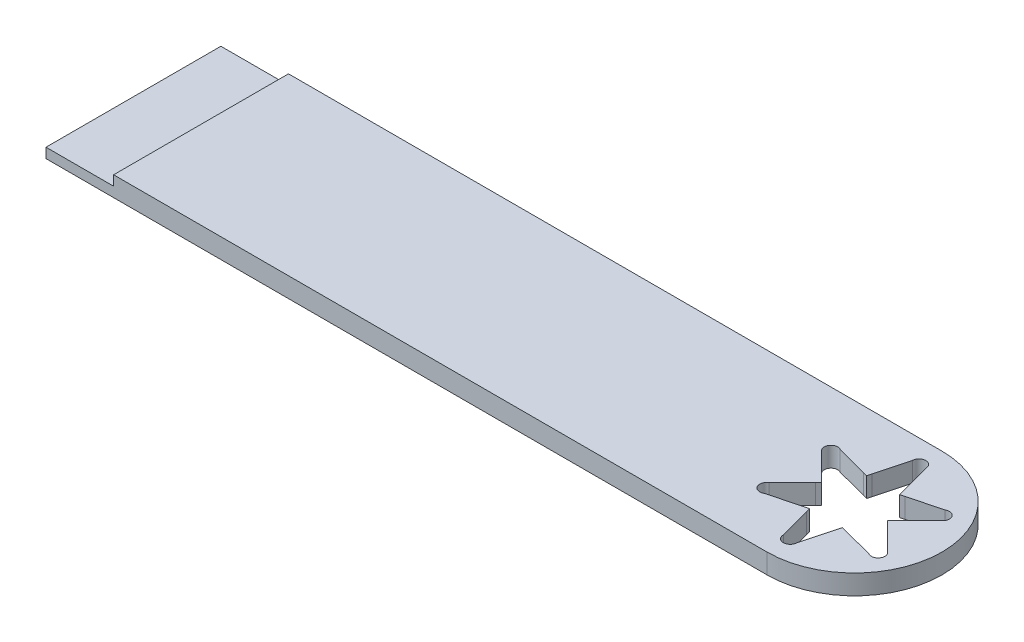
SolidWorks part; units mm, degrees
ref_plane "前基準面" through (0, 0, 0) normal (0, 0, 1) x (1, 0, 0)
ref_plane "上基準面" through (0, 0, 0) normal (0, 1, 0) x (1, 0, 0)
ref_plane "右基準面" through (0, 0, 0) normal (1, 0, 0) x (0, 0, -1)
sketch "草圖1" plane through (0, 0, 0) normal (0, 1, 0) x (1, 0, 0)
  circle A0 centre (0, 0) radius 15.8
  dimension "D1" = 31.6
extrude "填料-伸長1" add sketch "草圖1" along normal blind 4.4
sketch "草圖3" plane through (0, 0, 0) normal (0, -1, 0) x (1, 0, 0)
  line L0 (0, 15.8) -> (0, 15.7286) construction
  line L5 (0, 15.8) -> (0, 15.7286) construction
  line L9 (-1.5, 14.3) -> (-3.4, 7.2726)
  line L10 (-3.4, 7.2726) -> (-3.6501, 6.3221)
  line L13 (1.5, 14.3) -> (3.4, 7.2726)
  line L14 (3.4, 7.2726) -> (3.6501, 6.3221)
  line L15 (11.6342, 8.449) -> (4.5982, 6.5808)
  line L16 (13.1342, 5.851) -> (7.9982, 0.6918)
  line L17 (4.5982, 6.5808) -> (3.6501, 6.3221)
  line L18 (7.9982, 0.6918) -> (7.3001, 0)
  line L19 (13.1342, -5.851) -> (7.9982, -0.6918)
  line L20 (11.6342, -8.449) -> (4.5982, -6.5808)
  line L21 (7.9982, -0.6918) -> (7.3001, 0)
  line L22 (4.5982, -6.5808) -> (3.6501, -6.3221)
  line L23 (1.5, -14.3) -> (3.4, -7.2726)
  line L24 (-1.5, -14.3) -> (-3.4, -7.2726)
  line L25 (3.4, -7.2726) -> (3.6501, -6.3221)
  line L26 (-3.4, -7.2726) -> (-3.6501, -6.3221)
  line L27 (-11.6342, -8.449) -> (-4.5982, -6.5808)
  line L28 (-13.1342, -5.851) -> (-7.9982, -0.6918)
  line L29 (-4.5982, -6.5808) -> (-3.6501, -6.3221)
  line L30 (-7.9982, -0.6918) -> (-7.3001, 0)
  line L31 (-13.1342, 5.851) -> (-7.9982, 0.6918)
  line L32 (-11.6342, 8.449) -> (-4.5982, 6.5808)
  line L33 (-7.9982, 0.6918) -> (-7.3001, 0)
  line L34 (-4.5982, 6.5808) -> (-3.6501, 6.3221)
  circle A1 centre (0, 0) radius 15.8 construction
  arc A2 (0, 15.8) -> (-1.5, 14.3) centre (0, 14.3) ccw
  arc A3 (0, 15.8) -> (1.5, 14.3) centre (0, 14.3) cw
  arc A4 (13.6832, 7.9) -> (11.6342, 8.449) centre (12.3842, 7.15) ccw
  arc A5 (13.6832, 7.9) -> (13.1342, 5.851) centre (12.3842, 7.15) cw
  arc A6 (13.6832, -7.9) -> (13.1342, -5.851) centre (12.3842, -7.15) ccw
  arc A7 (13.6832, -7.9) -> (11.6342, -8.449) centre (12.3842, -7.15) cw
  arc A8 (0, -15.8) -> (1.5, -14.3) centre (0, -14.3) ccw
  arc A9 (0, -15.8) -> (-1.5, -14.3) centre (0, -14.3) cw
  arc A10 (-13.6832, -7.9) -> (-11.6342, -8.449) centre (-12.3842, -7.15) ccw
  arc A11 (-13.6832, -7.9) -> (-13.1342, -5.851) centre (-12.3842, -7.15) cw
  arc A12 (-13.6832, 7.9) -> (-13.1342, 5.851) centre (-12.3842, 7.15) ccw
  arc A13 (-13.6832, 7.9) -> (-11.6342, 8.449) centre (-12.3842, 7.15) cw
  point P12 (0, 14.3)
  point P69 (0, 0)
  dimension "D2" = 1.5
  dimension "D5" = 1.5
  dimension "D6" = 6
extrude "除料-伸長2" cut sketch "草圖3" against normal blind 4.4
sketch "草圖4" plane through (0, 0, 0) normal (0, 1, 0) x (1, 0, 0)
  circle A0 centre (0, 0) radius 15.8
  circle A1 centre (0, 0) radius 19.4
extrude "填料-伸長2" add sketch "草圖4" along normal blind 4.4
sketch "草圖5" plane through (0, 4.4, 0) normal (0, 1, 0) x (1, 0, 0)
  line L0 (0, 19.4) -> (0, -19.4) construction
  line L1 (0, 19.4) -> (-160, 19.4)
  line L2 (0, -19.4) -> (-160, -19.4)
  line L3 (-160, 19.4) -> (-160, -19.4)
  circle A0 centre (0, 0) radius 19.4 construction
  circle A2 centre (0, 0) radius 19.4
  arc A3 (0, 19.4) -> (0, -19.4) centre (0, 0) ccw
  dimension "D1" = 160
  dimension "D2" = 160
  dimension "D3" = 38.8
  dimension "D4" = 0
extrude "填料-伸長3" add sketch "草圖5" against normal blind 4.4
sketch "草圖6" plane through (0, 4.4, 0) normal (0, 1, 0) x (1, 0, 0)
  line L0 (-160, -19.4) -> (0, -19.4) construction
  line L1 (-160, 19.4) -> (-145, 19.4)
  line L2 (-160, 19.4) -> (-160, -19.4)
  line L3 (-160, -19.4) -> (-145, -19.4)
  line L4 (-145, 19.4) -> (-145, -19.4)
  dimension "D1" = 15
extrude "除料-伸長3" cut sketch "草圖6" against normal blind 2.2
